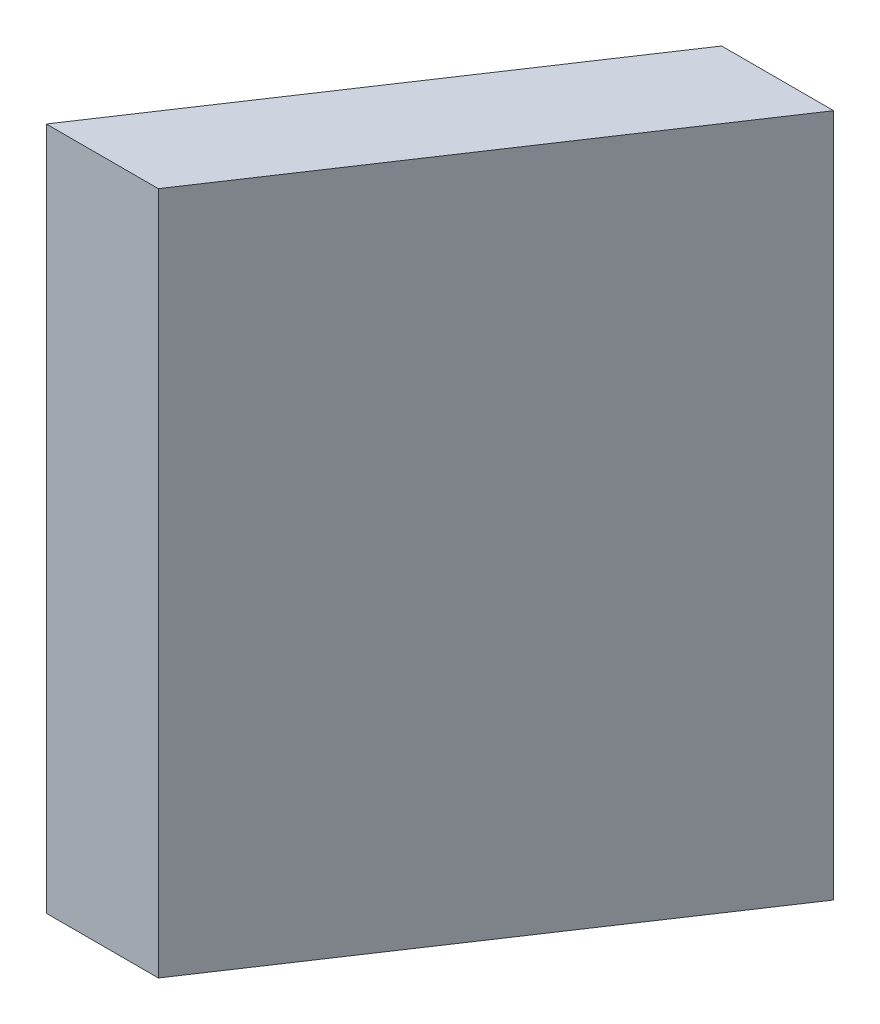
SolidWorks part; units mm, degrees
material "Custom Plastic"
ref_plane "Front Plane" through (0, 0, 0) normal (0, 0, 1) x (1, 0, 0)
ref_plane "Top Plane" through (0, 0, 0) normal (0, 1, 0) x (1, 0, 0)
ref_plane "Right Plane" through (0, 0, 0) normal (1, 0, 0) x (0, 0, -1)
sketch "Sketch1" plane through (0, 0, 0) normal (0, 1, 0) x (1, 0, 0)
  line L11 (0, 114886.8229) -> (109947.3759, 114886.8229) construction
  line L21 (109947.3759, 0) -> (109947.3759, 114886.8229) construction
  line L22 (1.3394, -6.5766) -> (35.4675, 44.6155) construction
  line L27 (39.049, 41.402) -> (11.4476, 0)
  line L28 (11.4476, 0) -> (0, 0)
  line L29 (39.049, 41.402) -> (27.6013, 41.402)
  line L30 (27.6013, 41.402) -> (0, 0)
  point P6 (33.3251, 41.402)
  point P9 (5.7238, 0)
  dimension "D1" = 9.525
  dimension "D2" = 41.402
  dimension "D3" = 56.31
extrude "Boss-Extrude1" add sketch "Sketch1" along normal blind 69.85
